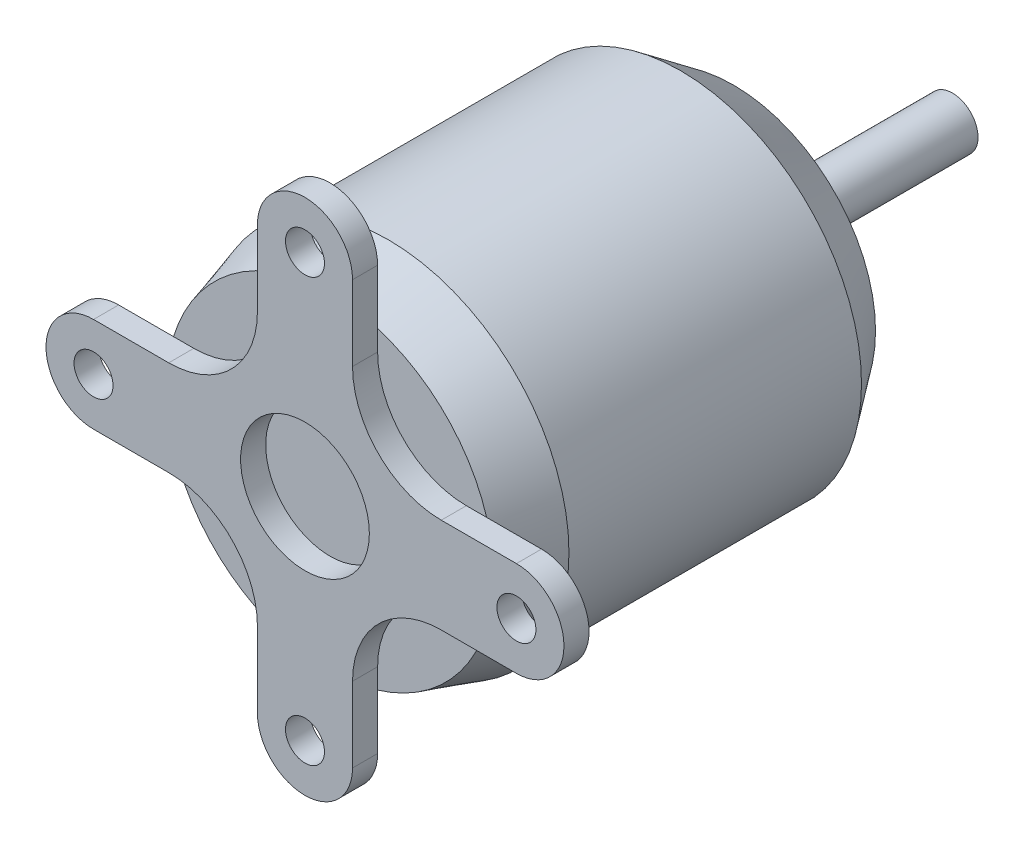
SolidWorks part; units mm, degrees
ref_plane "Front Plane" through (0, 0, 0) normal (0, 0, 1) x (1, 0, 0)
ref_plane "Top Plane" through (0, 0, 0) normal (0, 1, 0) x (1, 0, 0)
ref_plane "Right Plane" through (0, 0, 0) normal (1, 0, 0) x (0, 0, -1)
sketch "Sketch1" plane through (0, 0, 0) normal (1, 0, 0) x (0, 0, -1)
  line L0 (0, 0) -> (0, 12.5857)
  line L1 (0, 12.5857) -> (4.4704, 13.9065)
  line L2 (4.4704, 13.9065) -> (26.9748, 13.9065)
  line L3 (26.9748, 13.9065) -> (31.0388, 10.922)
  line L4 (31.0388, 10.922) -> (31.0388, 4.5022)
  line L5 (31.0388, 4.5022) -> (34.9758, 4.5022)
  line L6 (34.9758, 4.5022) -> (34.9758, 1.9685)
  line L7 (34.9758, 1.9685) -> (47.879, 1.9685)
  line L8 (47.879, 1.9685) -> (47.879, 0)
  line L9 (47.879, 0) -> (0, 0)
  line L10 (0, 0) -> (-24.4026, 0) construction
  line L11 (-1.9304, 0) -> (-1.9304, 22.6875) construction
  dimension "D1" = 25.1714
  dimension "D2" = 27.813
  dimension "D3" = 1.9304
  dimension "D4" = 36.9062
  dimension "D5" = 49.8094
  dimension "D6" = 3.937
  dimension "D7" = 9.0043
  dimension "D8" = 21.844
  dimension "D9" = 32.9692
  dimension "D10" = 6.4008
  dimension "D11" = 28.9052
revolve "Revolve1" add sketch "Sketch1" angle 360 about L10
sketch "Sketch2" plane through (0, 0, 0) normal (0, 0, 1) x (1, 0, 0)
  line L0 (0, 0) -> (0, 19.8638) construction
  line L1 (-3.6576, 16.265) -> (-3.6576, 3.6576)
  line L2 (3.6576, 16.265) -> (3.6576, 3.6576)
  line L3 (0, 0) -> (26.2579, 0) construction
  line L4 (3.6576, 3.6576) -> (10.4835, 3.6576)
  line L5 (-3.6576, 3.6576) -> (-10.4835, 3.6576)
  line L6 (0, 0) -> (-13.169, 13.169)
  line L7 (0, 0) -> (13.8763, 13.8763)
  circle A0 centre (0, 0) radius 4.953
  circle A1 centre (0, 16.265) radius 1.5
  arc A2 (3.6576, 16.265) -> (-3.6576, 16.265) centre (0, 16.265) ccw
  circle A3 centre (0, 0) radius 8 construction
  arc A4 (3.6576, 10.4835) -> (10.4835, 3.6576) centre (10.4835, 10.4835) ccw
  arc A5 (-3.6576, 10.4835) -> (-10.4835, 3.6576) centre (-10.4835, 10.4835) cw
  circle M8 centre (0, 0) radius 12.5857
  dimension "D1" = 7.3152
  dimension "D2" = 9.906
  dimension "D3" = 3
  dimension "D6" = 16
  dimension "D4" = 16.265
  dimension "D5" = 7.3152
extrude "Boss-Extrude1" add sketch "Sketch2" along normal blind 1.9304 contours A0 L7 L2 L1 L6 M8 | L1 A5 L6 | A4 L2 L7 | L2 A2 L1 A1 M8
pattern_circular "CirPattern1" count 4 over 360 about axis through (0, 0, 0) along (0, 0, 1) of "Boss-Extrude1"
